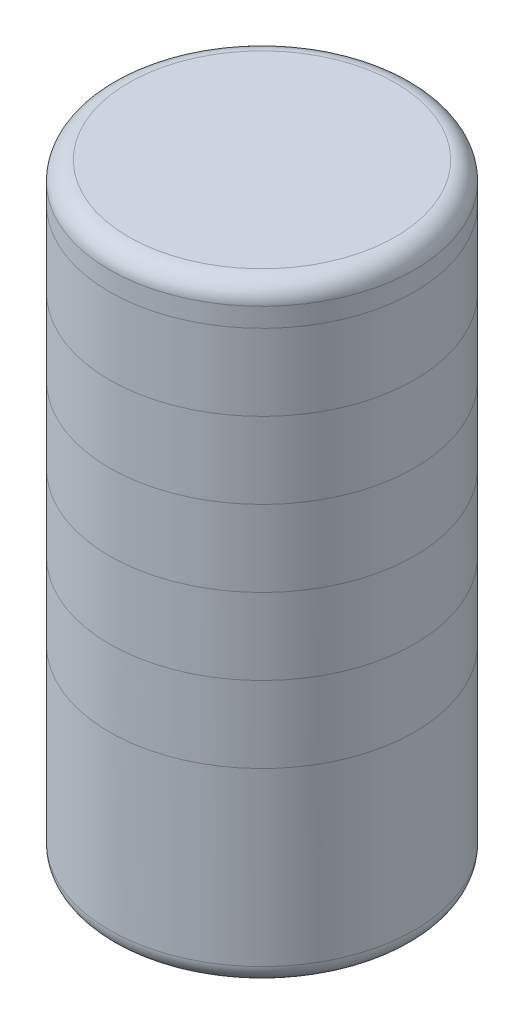
SolidWorks part; units mm, degrees
ref_plane "Front Plane" through (0, 0, 0) normal (0, 0, 1) x (1, 0, 0)
ref_plane "Top Plane" through (0, 0, 0) normal (0, 1, 0) x (1, 0, 0)
ref_plane "Right Plane" through (0, 0, 0) normal (1, 0, 0) x (0, 0, -1)
sketch "Sketch1" plane through (0, 0, 0) normal (0, 1, 0) x (1, 0, 0)
  circle A0 centre (0, 0) radius 25.4
  dimension "D1" = 50.8
extrude "Boss-Extrude1" add sketch "Sketch1" along normal blind 101.6
ref_plane "Plane1" through (0, 0, 25.4) normal (0, 0, 1) x (1, 0, 0)
sketch "Sketch3" plane through (0, 0, 25.4) normal (0, 0, 1) x (1, 0, 0)
  line L0 (-43.2516, 95.25) -> (51.2272, 95.25)
  line L1 (51.2272, 95.25) -> (51.2272, 31.75)
  line L2 (51.2272, 31.75) -> (-43.2516, 31.75)
  line L3 (-43.2516, 31.75) -> (-43.2516, 95.25)
  line L4 (-43.2516, 82.55) -> (51.2272, 82.55)
  line L5 (-43.2516, 69.85) -> (51.2272, 69.85)
  line L6 (-43.2516, 57.15) -> (51.2272, 57.15)
  line L7 (-43.2516, 44.45) -> (51.2272, 44.45)
  line L8 (25.4, 101.6) -> (-25.4, 101.6) construction
  dimension "D1" = 6.35
  dimension "D2" = 12.7
  dimension "D3" = 12.7
  dimension "D4" = 12.7
  dimension "D5" = 12.7
  dimension "D6" = 12.7
split line "Split Line2"
fillet "Fillet1" radius 3.175 1 edges at (0, 101.6, 25.4)
fillet "Fillet2" radius 3.175 1 edges at (0, 0, 25.4)
